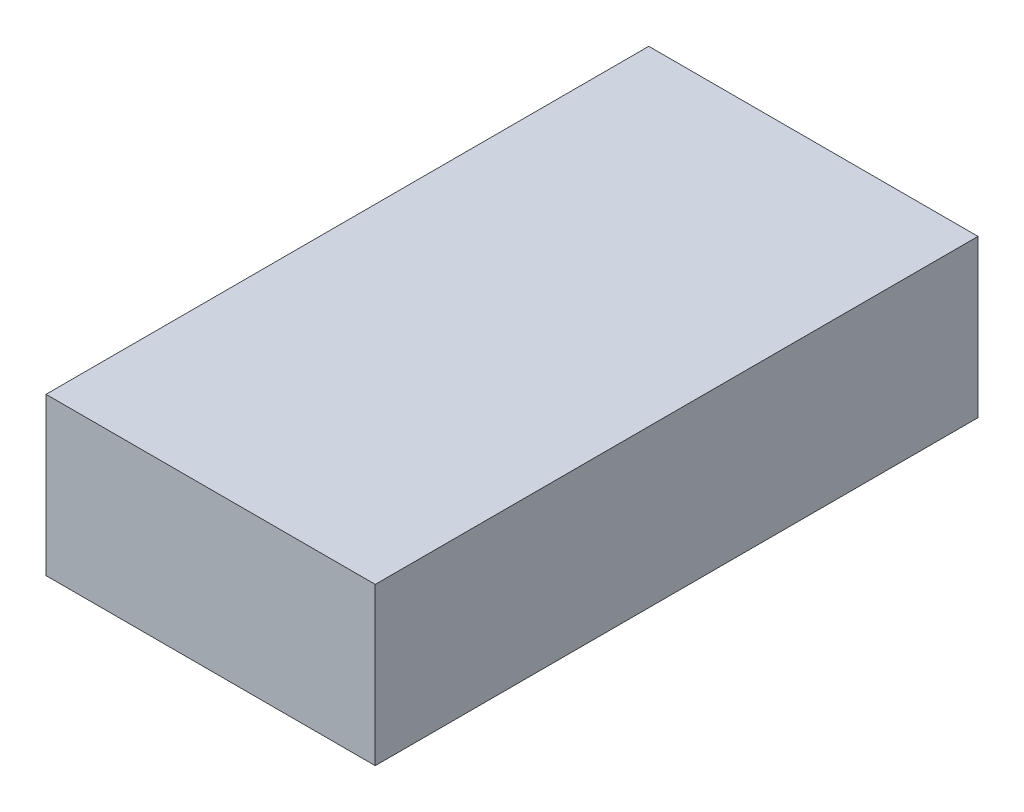
SolidWorks part; units mm, degrees
ref_plane "Front Plane" through (0, 0, 0) normal (0, 0, 1) x (1, 0, 0)
ref_plane "Top Plane" through (0, 0, 0) normal (0, 1, 0) x (1, 0, 0)
ref_plane "Right Plane" through (0, 0, 0) normal (1, 0, 0) x (0, 0, -1)
sketch "Sketch1" plane through (0, 0, 0) normal (0, 1, 0) x (1, 0, 0)
  line L1 (-16.25, -29.75) -> (16.25, -29.75)
  line L2 (-16.25, -29.75) -> (-16.25, 29.75)
  line L3 (-16.25, 29.75) -> (16.25, 29.75)
  line L4 (16.25, -29.75) -> (16.25, 29.75)
  line L5 (-16.25, -29.75) -> (16.25, 29.75) construction
  line L6 (-16.25, 29.75) -> (16.25, -29.75) construction
  point P0 (0, 0)
  dimension "D1" = 32.5
  dimension "D2" = 59.5
extrude "Boss-Extrude1" add sketch "Sketch1" along normal blind 15.5
